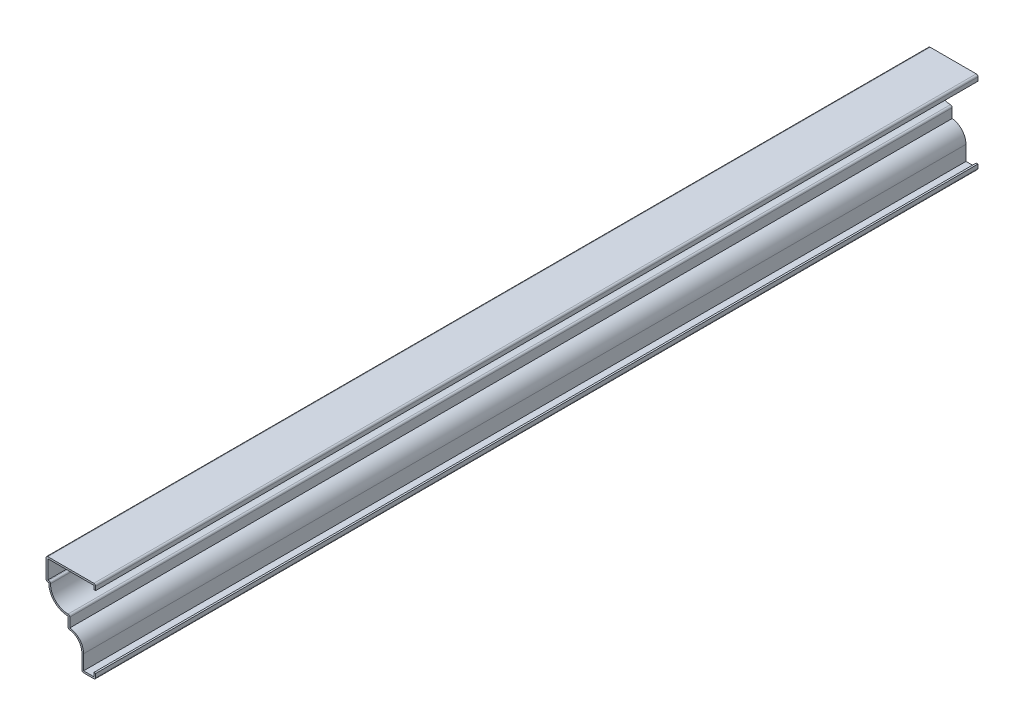
SolidWorks part; units mm, degrees
ref_plane "Front Plane" through (0, 0, 0) normal (0, 0, 1) x (1, 0, 0)
ref_plane "Top Plane" through (0, 0, 0) normal (0, 1, 0) x (1, 0, 0)
ref_plane "Right Plane" through (0, 0, 0) normal (1, 0, 0) x (0, 0, -1)
sketch "Sketch1" plane through (0, 0, 0) normal (0, 0, 1) x (1, 0, 0)
  line L0 (0, 0) -> (0, 47.625) construction
  line L1 (0, 3.175) -> (0, 0)
  line L2 (0, 0) -> (-7.9375, 0)
  line L3 (-7.9375, 0) -> (-7.9375, 9.525)
  line L4 (-15.875, 17.4625) -> (-15.875, 23.8125)
  line L5 (-26.9875, 34.925) -> (-28.575, 34.925)
  line L6 (-28.575, 34.925) -> (-28.575, 47.625)
  line L7 (-28.575, 47.625) -> (0, 47.625)
  line L8 (0, 47.625) -> (0, 44.45)
  arc A0 (-7.9375, 9.525) -> (-15.875, 17.4625) centre (-15.875, 9.525) ccw
  arc A1 (-15.875, 23.8125) -> (-26.9875, 34.925) centre (-15.875, 34.925) cw
  dimension "D4" = 7.9375
  dimension "D1" = 47.625
  dimension "D2" = 28.575
  dimension "D3" = 1.5875
  dimension "D5" = 7.9375
  dimension "D6" = 6.35
  dimension "D7" = 12.7
  dimension "D8" = 17.4625
  dimension "D9" = 3.175
extrude "Extrude-Thin1" add sketch "Sketch1" against normal blind 508 thin
fillet "Fillet1" radius 1.016 8 edges at (0, 47.625, -254) (-28.575, 47.625, -254) (-25.9203, 35.941, -254) (-28.575, 34.925, -254) (-14.859, 24.8797, -254) (-15.875, 17.4625, -254) (-7.9375, 0, -254) (0, 0, -254)
